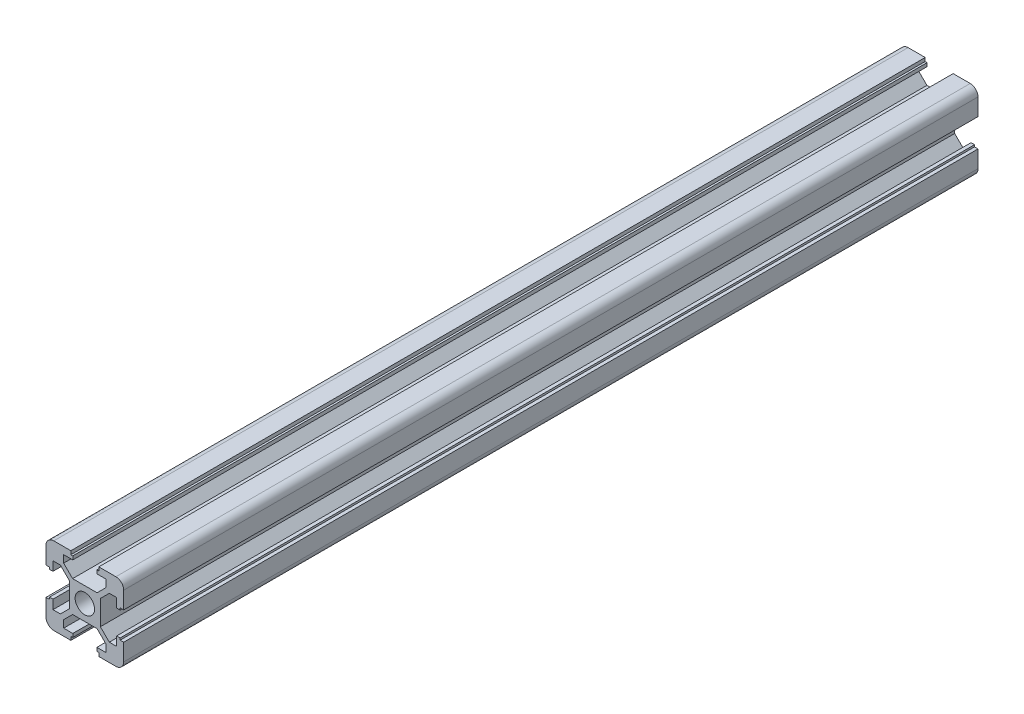
SolidWorks part; units mm, degrees
ref_plane "前视基准面" through (0, 0, 0) normal (0, 0, 1) x (1, 0, 0)
ref_plane "上视基准面" through (0, 0, 0) normal (0, 1, 0) x (1, 0, 0)
ref_plane "右视基准面" through (0, 0, 0) normal (1, 0, 0) x (0, 0, -1)
sketch "草图1" plane through (0, 0, 0) normal (0, 0, 1) x (1, 0, 0)
  line L0 (0, 0) -> (0, 12.7114) construction
  line L1 (0, 0) -> (12.7618, 0) construction
  line L2 (-3.1515, 4) -> (3.1515, 4)
  line L3 (0, 0) -> (12.1278, 12.1278) construction
  line L4 (3.1515, 4) -> (5.45, 6.2985)
  line L5 (5.45, 6.2985) -> (5.45, 8.2)
  line L6 (5.45, 8.2) -> (3.1, 8.2)
  line L7 (3.1, 8.2) -> (3.1, 9.1)
  line L8 (3.1, 9.1) -> (3.6, 9.1)
  line L9 (3.6, 9.1) -> (3.6, 10)
  line L10 (3.6, 10) -> (10, 10)
  line L11 (10, 3.6) -> (10, 10)
  line L12 (9.1, 3.6) -> (10, 3.6)
  line L13 (9.1, 3.1) -> (9.1, 3.6)
  line L14 (8.2, 3.1) -> (9.1, 3.1)
  line L15 (8.2, 5.45) -> (8.2, 3.1)
  line L16 (6.2985, 5.45) -> (8.2, 5.45)
  line L17 (4, 3.1515) -> (6.2985, 5.45)
  line L18 (4, -3.1515) -> (4, 3.1515)
  line L19 (4, -3.1515) -> (6.2985, -5.45)
  line L20 (6.2985, -5.45) -> (8.2, -5.45)
  line L21 (8.2, -5.45) -> (8.2, -3.1)
  line L22 (8.2, -3.1) -> (9.1, -3.1)
  line L23 (9.1, -3.1) -> (9.1, -3.6)
  line L24 (9.1, -3.6) -> (10, -3.6)
  line L25 (10, -3.6) -> (10, -10)
  line L26 (3.6, -10) -> (10, -10)
  line L27 (3.6, -9.1) -> (3.6, -10)
  line L28 (3.1, -9.1) -> (3.6, -9.1)
  line L29 (3.1, -8.2) -> (3.1, -9.1)
  line L30 (5.45, -8.2) -> (3.1, -8.2)
  line L31 (5.45, -6.2985) -> (5.45, -8.2)
  line L32 (3.1515, -4) -> (5.45, -6.2985)
  line L33 (-3.1515, -4) -> (3.1515, -4)
  line L34 (-3.1515, -4) -> (-5.45, -6.2985)
  line L35 (-5.45, -6.2985) -> (-5.45, -8.2)
  line L36 (-5.45, -8.2) -> (-3.1, -8.2)
  line L37 (-3.1, -8.2) -> (-3.1, -9.1)
  line L38 (-3.1, -9.1) -> (-3.6, -9.1)
  line L39 (-3.6, -9.1) -> (-3.6, -10)
  line L40 (-3.6, -10) -> (-10, -10)
  line L41 (-10, -3.6) -> (-10, -10)
  line L42 (-9.1, -3.6) -> (-10, -3.6)
  line L43 (-9.1, -3.1) -> (-9.1, -3.6)
  line L44 (-8.2, -3.1) -> (-9.1, -3.1)
  line L45 (-8.2, -5.45) -> (-8.2, -3.1)
  line L46 (-6.2985, -5.45) -> (-8.2, -5.45)
  line L47 (-4, -3.1515) -> (-6.2985, -5.45)
  line L48 (-4, -3.1515) -> (-4, 3.1515)
  line L49 (-4, 3.1515) -> (-6.2985, 5.45)
  line L50 (-6.2985, 5.45) -> (-8.2, 5.45)
  line L51 (-8.2, 5.45) -> (-8.2, 3.1)
  line L52 (-8.2, 3.1) -> (-9.1, 3.1)
  line L53 (-9.1, 3.1) -> (-9.1, 3.6)
  line L54 (-9.1, 3.6) -> (-10, 3.6)
  line L55 (-10, 3.6) -> (-10, 10)
  line L56 (-3.6, 10) -> (-10, 10)
  line L57 (-3.6, 9.1) -> (-3.6, 10)
  line L58 (-3.1, 9.1) -> (-3.6, 9.1)
  line L59 (-3.1, 8.2) -> (-3.1, 9.1)
  line L60 (-5.45, 8.2) -> (-3.1, 8.2)
  line L61 (-5.45, 6.2985) -> (-5.45, 8.2)
  line L62 (-3.1515, 4) -> (-5.45, 6.2985)
  circle A0 centre (0, 0) radius 2.5
  point P5 (-4, 0)
  point P24 (4, 0)
  point P40 (0, -4)
  point P69 (0, 4)
  dimension "D9" = 5
  dimension "D1" = 4
  dimension "D2" = 0.6
  dimension "D3" = 5.45
  dimension "D4" = 8.2
  dimension "D5" = 3.1
  dimension "D6" = 3.6
  dimension "D7" = 0.9
  dimension "D8" = 1.8
extrude "凸台-拉伸1" add sketch "草图1" along normal blind 220
fillet "圆角1" radius 2 4 edges at (10, -10, 110) (-10, -10, 110) (-10, 10, 110) (10, 10, 110)
